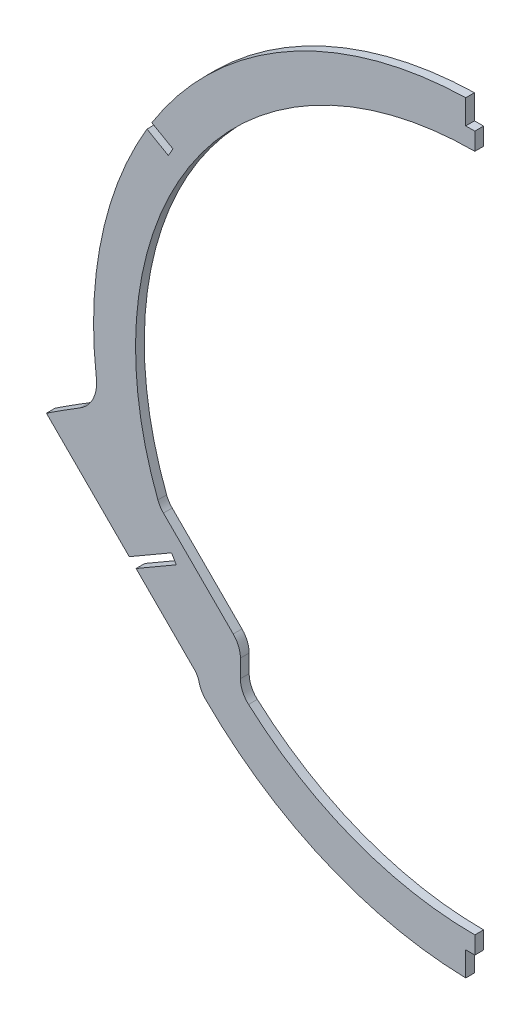
SolidWorks part; units mm, degrees
material "Plywood"
ref_plane "Front Plane" through (0, 0, 0) normal (0, 0, 1) x (1, 0, 0)
ref_plane "Top Plane" through (0, 0, 0) normal (0, 1, 0) x (1, 0, 0)
ref_plane "Right Plane" through (0, 0, 0) normal (1, 0, 0) x (0, 0, -1)
sketch "Sketch1" plane through (0, 0, 0) normal (0, 0, 1) x (1, 0, 0)
  line L0 (0, 32.094) -> (0, -346.2619) construction
  line L1 (0, 0) -> (0, 244.345) construction
  line L2 (0, 0) -> (0, 471.6969) construction
  line L3 (0, 0) -> (-283.5939, 0) construction
  line L4 (-127.2933, -32.5553) -> (-100.3525, -59.496)
  line L5 (-100.3525, -59.496) -> (-100.3525, -73.5092)
  line L6 (-100.3525, -59.496) -> (-54.3993, -105.4493) construction
  arc A0 (-54.3993, -105.4493) -> (-127.2933, -32.5553) centre (0, 21.844) ccw
  arc A2 (-100.3525, -73.5092) -> (-54.3993, -105.4493) centre (0, 21.844) ccw construction
  arc A3 (-127.2933, -32.5553) -> (-100.3525, -73.5092) centre (0, 21.844) ccw construction
  arc A4 (-100.3525, -73.5092) -> (-54.3993, -105.4493) centre (0, 21.844) ccw
  spline S2 degree 3 poles (-727.3087, -4752.7911) (287.5763, -944.0707) (320.9183, 35.1812) (49.9381, 150.9258) (45.7097, 152.4909) (37.1079, 155.2035) (32.7346, 156.3511) (27.1752, 157.5183) (26.0587, 157.7384) (23.8163, 158.1514) (22.6888, 158.3447) (19.306, 158.8811) (17.0511, 159.1813) (10.2867, 159.9126) (1.2693, 160.4377) (-7.745, 160.0789) (-14.5046, 159.4749) (-16.7575, 159.2176) (-20.1367, 158.7464) (-21.263, 158.5751) (-23.5156, 158.2037) (-24.6421, 158.0036) (-30.2426, 156.9366) (-34.6466, 155.8674) (-43.3063, 153.3113) (-47.562, 151.8242) (-55.9254, 148.4331) (-60.0331, 146.529) (-66.0807, 143.3516) (-68.0818, 142.2359) (-72.0044, 139.9197) (-73.9301, 138.7173) (-79.6017, 134.9792) (-86.884, 129.6473) (-93.6143, 123.6295) (-98.4521, 118.8554) (-100.0296, 117.2204) (-102.3424, 114.7015) (-103.1054, 113.8496) (-104.6077, 112.1297) (-105.3467, 111.2623) (-108.9818, 106.8875) (-111.6981, 103.2683) (-116.7574, 95.7975) (-119.1004, 91.9459) (-123.4121, 84.0098) (-125.3809, 79.9253) (-127.6006, 74.6695) (-128.0327, 73.61) (-128.8681, 71.4874) (-129.2719, 70.423) (-130.4422, 67.2205) (-131.1674, 65.0732) (-133.1812, 58.5951) (-135.4347, 49.861) (-136.834, 40.9354) (-137.5569, 34.168) (-137.7434, 31.9) (-137.9397, 28.4793) (-137.9911, 27.3374) (-138.0656, 25.0596) (-138.0887, 23.9223) (-138.135, 18.2442) (-137.9496, 13.7276) (-137.1441, 4.7454) (-136.5239, 0.2797) (-134.8456, -8.6005) (-133.7876, -13.015) (-131.2181, -21.791) (-129.7278, -26.0794) (-126.351, -34.4622) (-124.4643, -38.5569) (-120.2966, -46.5538) (-118.0156, -50.456) (-114.9122, -55.2108) (-114.2789, -56.1556) (-112.9868, -58.0327) (-112.3272, -58.9661) (-110.315, -61.7398) (-108.9333, -63.5482) (-104.6702, -68.8537) (-98.6716, -75.6089) (-92.0553, -81.7381) (-86.8592, -86.0978) (-85.0881, -87.5114) (-82.3719, -89.5716) (-81.4566, -90.2482) (-79.6058, -91.5811) (-78.6696, -92.238) (231.9603, -304.4561) (1345.3057, 781.0624) (3419.1463, 3416.8041) knots -1.975241 -1.975241 -1.975241 -1.975241 0.03125 0.03125 0.0625 0.0625 0.09375 0.09375 0.101563 0.101563 0.109375 0.109375 0.125 0.125 0.15625 0.1875 0.1875 0.203125 0.203125 0.210937 0.210937 0.21875 0.21875 0.25 0.25 0.28125 0.28125 0.3125 0.3125 0.328125 0.328125 0.34375 0.34375 0.375 0.40625 0.40625 0.421875 0.421875 0.429687 0.429687 0.4375 0.4375 0.46875 0.46875 0.5 0.5 0.53125 0.53125 0.539062 0.539062 0.546875 0.546875 0.5625 0.5625 0.59375 0.625 0.625 0.640625 0.640625 0.648437 0.648437 0.65625 0.65625 0.6875 0.6875 0.71875 0.71875 0.75 0.75 0.78125 0.78125 0.8125 0.8125 0.84375 0.84375 0.851562 0.851562 0.859375 0.859375 0.875 0.875 0.90625 0.9375 0.9375 0.953125 0.953125 0.960937 0.960937 0.96875 0.96875 3.533217 3.533217 3.533217 3.533217 only from (66.3397, 143.1887) to (-66.0465, -100.0388)
  spline S3 degree 3 poles (66.3397, 143.1887) (62.3323, 145.3909) (58.2494, 147.3758) (49.9381, 150.9258) (45.7097, 152.4909) (37.1079, 155.2035) (32.7346, 156.3511) (27.1752, 157.5183) (26.0587, 157.7384) (23.8163, 158.1514) (22.6888, 158.3447) (19.306, 158.8811) (17.0511, 159.1813) (10.2867, 159.9126) (1.2693, 160.4377) (-7.745, 160.0789) (-14.5046, 159.4749) (-16.7575, 159.2176) (-20.1367, 158.7464) (-21.263, 158.5751) (-23.5156, 158.2037) (-24.6421, 158.0036) (-30.2426, 156.9366) (-34.6466, 155.8674) (-43.3063, 153.3113) (-47.562, 151.8242) (-55.9254, 148.4331) (-60.0331, 146.529) (-66.0807, 143.3516) (-68.0818, 142.2359) (-72.0044, 139.9197) (-73.9301, 138.7173) (-79.6017, 134.9792) (-86.884, 129.6473) (-93.6143, 123.6295) (-98.4521, 118.8554) (-100.0296, 117.2204) (-102.3424, 114.7015) (-103.1054, 113.8496) (-104.6077, 112.1297) (-105.3467, 111.2623) (-108.9818, 106.8875) (-111.6981, 103.2683) (-116.7574, 95.7975) (-119.1004, 91.9459) (-123.4121, 84.0098) (-125.3809, 79.9253) (-127.6006, 74.6695) (-128.0327, 73.61) (-128.8681, 71.4874) (-129.2719, 70.423) (-130.4422, 67.2205) (-131.1674, 65.0732) (-133.1812, 58.5951) (-135.4347, 49.861) (-136.834, 40.9354) (-137.5569, 34.168) (-137.7434, 31.9) (-137.9397, 28.4793) (-137.9911, 27.3374) (-138.0656, 25.0596) (-138.0887, 23.9223) (-138.135, 18.2442) (-137.9496, 13.7276) (-137.1441, 4.7454) (-136.5239, 0.2797) (-134.8456, -8.6005) (-133.7876, -13.015) (-131.2181, -21.791) (-129.7278, -26.0794) (-127.6847, -31.1513) (-127.3213, -32.0275) (-126.9491, -32.8995) knots 0 0 0 0 0.03125 0.03125 0.0625 0.0625 0.09375 0.09375 0.101563 0.101563 0.109375 0.109375 0.125 0.125 0.15625 0.1875 0.1875 0.203125 0.203125 0.210937 0.210937 0.21875 0.21875 0.25 0.25 0.28125 0.28125 0.3125 0.3125 0.328125 0.328125 0.34375 0.34375 0.375 0.40625 0.40625 0.421875 0.421875 0.429687 0.429687 0.4375 0.4375 0.46875 0.46875 0.5 0.5 0.53125 0.53125 0.539062 0.539062 0.546875 0.546875 0.5625 0.5625 0.59375 0.625 0.625 0.640625 0.640625 0.648437 0.648437 0.65625 0.65625 0.6875 0.6875 0.71875 0.71875 0.75 0.75 0.78125 0.78125 0.787815 0.787815 0.787815 0.787815 construction
  point P2 (0, 160.2226)
  point P3 (0, -116.9127)
  point P23 (-100.3525, -59.496)
  dimension "D1" = 277.1353
  dimension "D2" = 276.86
  dimension "D3" = 21.844
  dimension "D5" = 45
  dimension "D6" = 113.03
  dimension "D4" = 38.1
  dimension "D7" = 45
extrude "Boss-Extrude1" add sketch "Sketch1" along normal mid plane 3.175
sketch "Sketch2" plane through (0, 0, 1.5875) normal (0, 0, 1) x (1, 0, 0)
  line L2 (-114.3729, -23.9231) -> (-85.1125, -53.1834)
  line L3 (-114.3729, -23.9231) -> (-85.1125, -53.1834)
  line L4 (-85.1125, -53.1834) -> (-85.1125, -67.2157)
  line L5 (-85.1125, -53.1834) -> (-85.1125, -67.2157)
  arc A2 (-85.1125, -67.2157) -> (-114.3729, -23.9231) centre (0, 21.844) ccw
  arc A3 (-85.1125, -67.2157) -> (-114.3729, -23.9231) centre (0, 21.844) ccw
  dimension "D1" = 15.24
extrude "Cut-Extrude1" cut sketch "Sketch2" against normal up to surface (3.175 mm away) up to face at (-32.8418, -4.8687, -1.5875)
fillet "Fillet1" radius 8.89 6 edges at (-127.2933, -32.5553, 0) (-114.3729, -23.9231, 0) (-100.3525, -59.496, 0) (-100.3525, -73.5092, 0) (-85.1125, -53.1834, 0) (-85.1125, -67.2157, 0)
sketch "Sketch3" plane through (0, 0, 1.5875) normal (0, 0, 1) x (1, 0, 0)
  line L0 (-0.0002, 49.9919) -> (-0.0176, 733.2) construction
  line L1 (-0.0002, 49.9919) -> (-0.0176, 733.2) construction
  line L2 (-136.2041, -28.3557) -> (-0.0002, 49.9919) construction
  line L3 (136.2076, -28.3488) -> (-0.0002, 49.9919) construction
  line L4 (-136.2041, -28.3557) -> (-0.0002, 49.9919) construction
  line L5 (136.2076, -28.3488) -> (-0.0002, 49.9919) construction
  line L6 (-1.6539, 152.6441) -> (-1.654, 160.2641)
  line L7 (1.6481, 152.6442) -> (1.648, 160.2642)
  line L8 (-1.6539, 152.6441) -> (1.6481, 152.6442)
  line L9 (119.8485, -45.962) -> (106.7537, -38.3747)
  line L10 (121.4435, -43.2066) -> (108.3479, -35.6188)
  line L18 (121.4435, -43.2066) -> (108.3479, -35.6188)
  line L30 (-123.167, -47.8929) -> (-104.8722, -37.2914)
  line L35 (119.8485, -45.962) -> (106.7537, -38.3747)
  line L47 (108.5244, -35.721) -> (120.1169, -46.1175) construction
  line L48 (114.3206, -40.9193) -> (126.5619, -48.0121) construction
  line L49 (113.8577, -42.5592) -> (122.0137, -47.2849)
  line L50 (115.5132, -39.7021) -> (123.6691, -44.4278)
  line L51 (113.8577, -42.5592) -> (115.5132, -39.7021)
  line L52 (122.0137, -47.2849) -> (123.6691, -44.4278)
  line L58 (-124.7703, -45.1423) -> (-106.4681, -34.5364)
  line L59 (-124.7703, -45.1423) -> (-123.167, -47.8929)
  line L71 (-124.7703, -45.1423) -> (-123.167, -47.8929) construction
  line L72 (-124.7703, -45.1423) -> (-106.4681, -34.5364) construction
  line L73 (-123.167, -47.8929) -> (-104.8722, -37.2914) construction
  line L74 (-123.167, -47.8929) -> (-107.9499, -35.3951) construction
  line L75 (-115.5584, -41.644) -> (-110.9064, -38.9482) construction
  line L76 (-119.3826, -41.9518) -> (-112.6266, -38.0369)
  line L77 (-117.727, -44.8088) -> (-110.971, -40.8938)
  line L78 (-119.3826, -41.9518) -> (-117.727, -44.8088)
  line L79 (-112.6266, -38.0369) -> (-110.971, -40.8938)
  arc A0 (-54.3993, -105.4493) -> (-127.2933, -32.5553) centre (0, 21.844) ccw construction
  arc A2 (-1.654, 160.2641) -> (-130.2816, -24.9489) centre (0, 21.844) ccw construction
  arc A3 (-130.2816, -24.9489) -> (-127.2933, -32.5553) centre (0, 21.844) ccw construction
  arc A4 (-1.654, 160.2641) -> (-130.2816, -24.9489) centre (0, 21.844) ccw construction
  arc A5 (-130.2816, -24.9489) -> (-127.9919, -30.8906) centre (0, 21.844) ccw construction
  arc A14 (130.2841, -24.9419) -> (1.648, 160.2642) centre (0, 21.844) ccw construction
  arc A15 (1.648, 160.2642) -> (-1.654, 160.2641) centre (0, 21.844) ccw
  arc A16 (130.2841, -24.9419) -> (1.648, 160.2642) centre (0, 21.844) ccw construction
  arc A17 (1.648, 160.2642) -> (-1.654, 160.2641) centre (0, 21.844) ccw
  spline S0 degree 3 poles (106.7537, -38.3747) (107.2851, -37.456) (107.8165, -36.5374) (108.3479, -35.6188) knots 0 0 0 0 1 1 1 1 weights 1 1 1 1
  spline S1 degree 3 poles (119.8485, -45.962) (120.3802, -45.0435) (120.9118, -44.1251) (121.4435, -43.2066) knots 0 0 0 0 1 1 1 1 weights 1 1 1 1
  spline S2 degree 3 poles (-3847.6145, -6688.6752) (-1193.4125, -2388.6207) (1509.1801, 2280.5122) (3904.1617, 6703.7111) knots -2509.987289 -2509.987289 -2509.987289 -2509.987289 2515.773198 2515.773198 2515.773198 2515.773198 weights 1.033987 0.988628 0.988671 1.034116 only from (119.8485, -45.962) to (121.4435, -43.2066)
  spline S3 degree 3 poles (-3959.2479, 6785.3642) (-1478.3785, 2275.755) (1214.3062, -2372.48) (3895.1026, -6773.1419) knots -2513.009721 -2513.009721 -2513.009721 -2513.009721 2512.935792 2512.935792 2512.935792 2512.935792 weights 1.021221 0.992932 0.992926 1.021203 only from (-106.4681, -34.5364) to (-104.8722, -37.2914)
  spline S4 degree 3 poles (-106.4681, -34.5364) (-105.9361, -35.4547) (-105.4042, -36.373) (-104.8722, -37.2914) knots 0 0 0 0 1 1 1 1 weights 1 1 1 1 construction
  spline S6 degree 3 poles (-3867.0162, -6706.7922) (-1202.4386, -2371.9097) (1495.677, 2292.8781) (3905.6981, 6731.4638) knots -2508.399086 -2508.399086 -2508.399086 -2508.399086 2517.428296 2517.428296 2517.428296 2517.428296 weights 1.03062 0.989729 0.989792 1.030818 only from (106.7537, -38.3747) to (108.3479, -35.6188)
  point P49 (-116.0256, -43.8229)
  point P50 (120.451, -46.3794)
  dimension "D1" = 3.302
  dimension "D2" = 7.62
  dimension "D4" = 3.302
  dimension "D5" = 7.62
  dimension "D6" = 3.302
  dimension "D7" = 5.842
sketch "Sketch4" plane through (0, 0, 0) normal (1, 0, 0) x (0, 0, -1)
  line L1 (-96.2805, 232.7957) -> (122.2438, 232.7957)
  line L2 (-96.2805, 232.7957) -> (-96.2805, -207.8589)
  line L3 (-96.2805, -207.8589) -> (122.2438, -207.8589)
  line L4 (122.2438, 232.7957) -> (122.2438, -207.8589)
extrude "Cut-Extrude3" cut sketch "Sketch4" along normal through all
sketch "Sketch5" plane through (0, 0, 0) normal (0, 0, 1) x (1, 0, 0)
  line L0 (0, 0) -> (-220.3195, 0) construction
  line L3 (-100.3441, -70.2779) -> (-93.132, -63.0671)
  line L4 (-100.3441, -70.2779) -> (-155.5427, -15.0686)
  line L5 (-93.132, -63.0671) -> (-135.3862, -2.54)
  arc A0 (-100.3525, -69.8905) -> (-97.7394, -76.186) centre (-91.4625, -69.8905) ccw construction
  arc A1 (-135.3862, -2.54) -> (-155.5427, -15.0686) centre (85.5484, -380.4649) ccw
  dimension "D3" = 437.7663
  dimension "D1" = 120.65
  dimension "D2" = 45.006
  dimension "D4" = 135.3862
  dimension "D5" = 2.54
  dimension "D6" = 15.0686
extrude "Boss-Extrude2" add sketch "Sketch5" along normal mid plane 3.175
fillet "Fillet2" radius 12.7 1 edges at (-136.1813, -3.0059, 0)
fillet "Fillet3" radius 6.35 1 edges at (-100.3441, -70.2779, 0)
sketch "Sketch6" plane through (0, 0, -1.5875) normal (0, 0, -1) x (-1, 0, 0)
  line L0 (0, 0) -> (0, 145.034) construction
  line L1 (0, 145.034) -> (0, 151.384) construction
  line L2 (0, 145.034) -> (0, 160.274) construction
  line L3 (104.929, 86.3862) -> (0, 26.2525) construction
  line L4 (0, 151.384) -> (3.302, 151.384)
  line L5 (0, 151.384) -> (0, 164.084)
  line L6 (0, 164.084) -> (3.302, 164.084)
  line L7 (3.302, 151.384) -> (3.302, 164.084)
  line L14 (104.929, 86.3862) -> (110.4384, 89.5435) construction
  line L15 (109.5985, 91.009) -> (111.2782, 88.078)
  line L16 (109.5985, 91.009) -> (120.6173, 97.3238)
  line L17 (111.2782, 88.078) -> (122.297, 94.3928)
  line L18 (120.6173, 97.3238) -> (122.297, 94.3928)
  line L26 (103.7614, -34.5345) -> (0, 25.5937) construction
  line L27 (103.7614, -34.5345) -> (109.2556, -37.7183) construction
  line L28 (108.4087, -39.1798) -> (110.1025, -36.2569)
  line L29 (108.4087, -39.1798) -> (124.8912, -48.7311)
  line L30 (110.1025, -36.2569) -> (126.585, -45.8082)
  line L31 (124.8912, -48.7311) -> (126.585, -45.8082)
  line L32 (0, 0) -> (0, -101.346) construction
  line L33 (0, -101.346) -> (0, -107.696) construction
  line L36 (0, -107.696) -> (3.302, -107.696)
  line L37 (0, -107.696) -> (0, -120.396)
  line L38 (0, -120.396) -> (3.302, -120.396)
  line L39 (3.302, -107.696) -> (3.302, -120.396)
  point P3 (110.4384, 89.5435)
  point P15 (109.2556, -37.7183)
  dimension "D13" = 6.35
  dimension "D1" = 151.384
  dimension "D2" = 12.7
  dimension "D3" = 3.302
  dimension "D4" = 60.183
  dimension "D5" = 26.2525
  dimension "D6" = 120.9386
  dimension "D7" = 6.35
  dimension "D8" = 3.3782
  dimension "D9" = 12.7
  dimension "D10" = 59.908
  dimension "D11" = 25.5937
  dimension "D12" = 119.9243
  dimension "D14" = 3.3782
  dimension "D15" = 19.05
  dimension "D16" = 6.35
  dimension "D17" = 107.696
  dimension "D18" = 12.7
  dimension "D19" = 3.302
extrude "Cut-Extrude4" cut sketch "Sketch6" against normal through all
equation "\"a\"= 0.06"
equation "\"slotwidth\"=0.13"
equation "\"slotheight\"=0.3"
